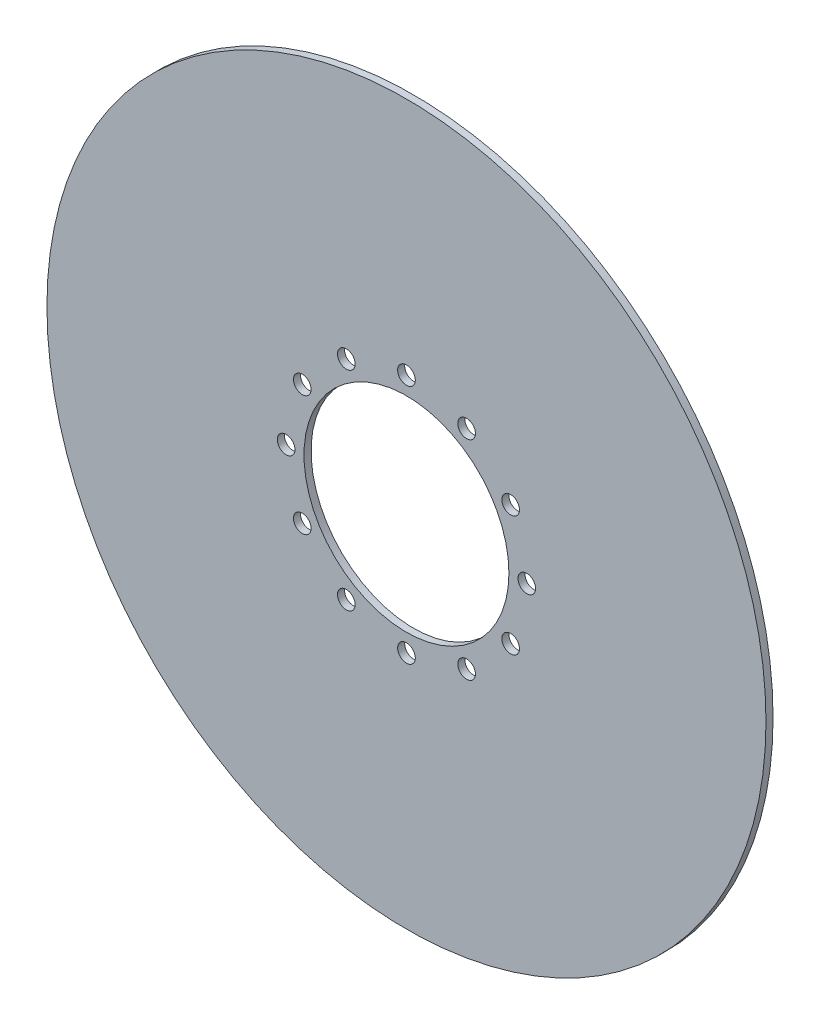
SolidWorks part; units mm, degrees
material "AISI 1020"
ref_plane "Front Plane" through (0, 0, 0) normal (0, 0, 1) x (1, 0, 0)
ref_plane "Top Plane" through (0, 0, 0) normal (0, 1, 0) x (1, 0, 0)
ref_plane "Right Plane" through (0, 0, 0) normal (1, 0, 0) x (0, 0, -1)
sketch "Sketch1" plane through (0, 0, 0) normal (0, 0, 1) x (1, 0, 0)
  circle A0 centre (0, 0) radius 101.6
  circle A1 centre (0, 0) radius 28.956
  circle A2 centre (0, 0) radius 34 construction
  circle A3 centre (0, 34) radius 2.497
  circle A4 centre (17, 29.4449) radius 2.497
  circle A5 centre (29.4449, 17) radius 2.497
  circle A6 centre (34, 0) radius 2.497
  circle A7 centre (29.4449, -17) radius 2.497
  circle A8 centre (17, -29.4449) radius 2.497
  circle A9 centre (0, -34) radius 2.497
  circle A10 centre (-17, -29.4449) radius 2.497
  circle A11 centre (-29.4449, -17) radius 2.497
  circle A12 centre (-34, 0) radius 2.497
  circle A13 centre (-29.4449, 17) radius 2.497
  circle A14 centre (-17, 29.4449) radius 2.497
  point P32 (0, 0)
  dimension "D1" = 203.2
  dimension "D2" = 57.912
  dimension "D3" = 68
  dimension "D4" = 12
extrude "Boss-Extrude1" add sketch "Sketch1" along normal blind 2
move or copy body "Body-Move/Copy2" [suppressed] bodies to move or copy 101
move or copy body "Body-Move/Copy1" [suppressed] bodies to move or copy 101
